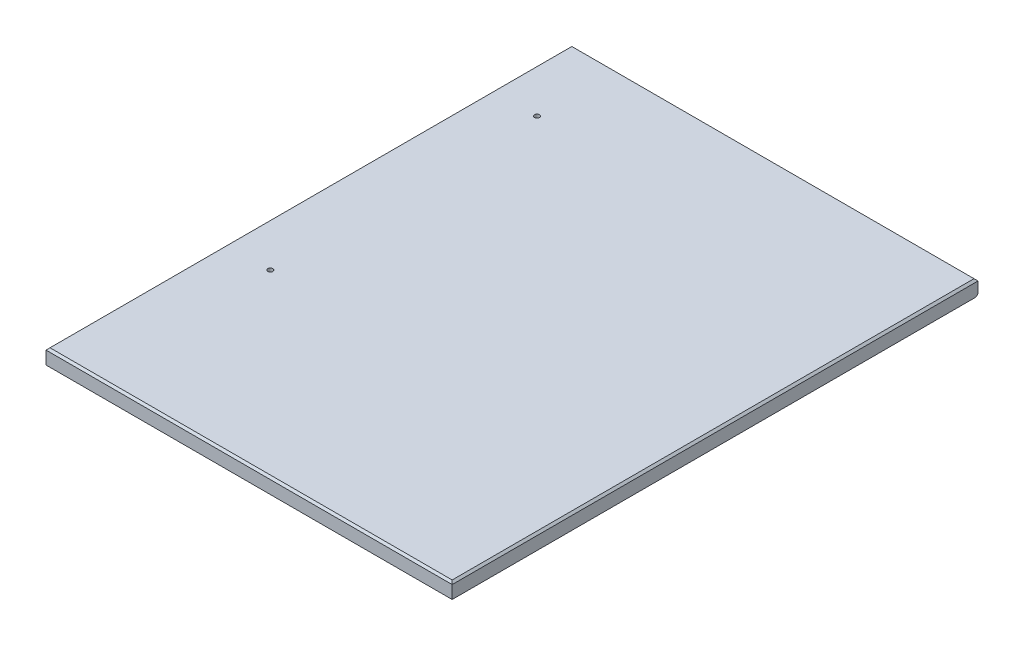
SolidWorks part; units mm, degrees
material "Oak"
ref_plane "Front Plane" through (0, 0, 0) normal (0, 0, 1) x (1, 0, 0)
ref_plane "Top Plane" through (0, 0, 0) normal (0, 1, 0) x (1, 0, 0)
ref_plane "Right Plane" through (0, 0, 0) normal (1, 0, 0) x (0, 0, -1)
sketch "Sketch1" plane through (0, 0, 0) normal (0, 1, 0) x (1, 0, 0)
  line L1 (0, 0) -> (517.4488, 0)
  line L2 (0, 0) -> (0, 669.925)
  line L3 (0, 669.925) -> (517.4488, 669.925)
  line L4 (517.4488, 0) -> (517.4488, 669.925)
  dimension "D1" = 669.925
  dimension "D2" = 517.4488
extrude "Boss-Extrude1" add sketch "Sketch1" along normal blind 19.05
chamfer "Chamfer1" distance 2.54 angle 45 4 edges at (258.7244, 19.05, -669.925) (517.4488, 19.05, -334.9625) (258.7244, 19.05, 0) (0, 19.05, -334.9625)
chamfer "Chamfer2" distance 2.54 angle 45 1 edges at (258.7244, 0, -669.925)
sketch "Sketch2" plane through (0, 19.05, 0) normal (0, 1, 0) x (1, 0, 0)
  line L1 (57.15, 568.325) -> (666.75, 568.325) construction
  line L2 (57.15, 568.325) -> (57.15, 228.6) construction
  line L3 (57.15, 228.6) -> (666.75, 228.6) construction
  line L4 (666.75, 568.325) -> (666.75, 228.6) construction
  circle A1 centre (57.15, 568.325) radius 3.175
  circle A3 centre (57.15, 228.6) radius 3.175
  circle A5 centre (666.75, 568.325) radius 3.175
  circle A7 centre (666.75, 228.6) radius 3.175
  dimension "D1" = 6.35
  dimension "D2" = 609.6
  dimension "D3" = 339.725
  dimension "D4" = 228.6
  dimension "D5" = 57.15
extrude "Cut-Extrude1" cut sketch "Sketch2" against normal through all
